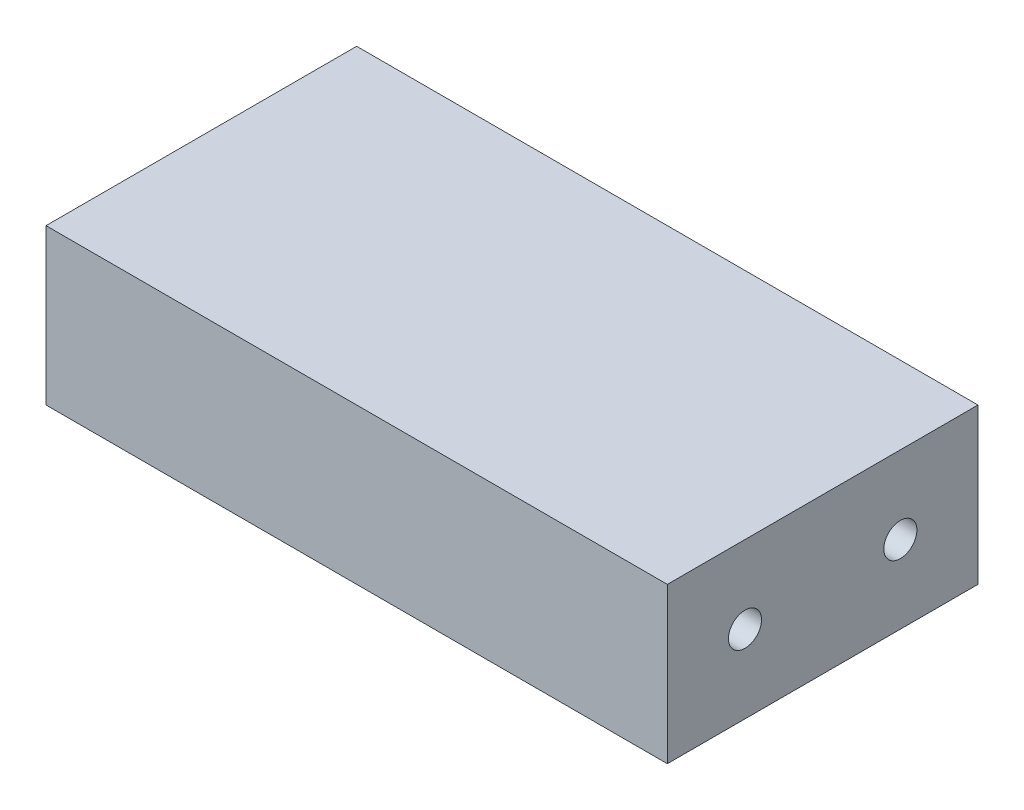
SolidWorks part; units mm, degrees
ref_plane "Front Plane" through (0, 0, 0) normal (0, 0, 1) x (1, 0, 0)
ref_plane "Top Plane" through (0, 0, 0) normal (0, 1, 0) x (1, 0, 0)
ref_plane "Right Plane" through (0, 0, 0) normal (1, 0, 0) x (0, 0, -1)
sketch "Sketch1" plane through (0, 0, 0) normal (0, 1, 0) x (1, 0, 0)
  line L0 (-26, 19.0667) -> (-26, -6.3333)
  line L1 (-26, -6.3333) -> (24.8, -6.3333)
  line L2 (24.8, -6.3333) -> (24.8, 19.0667)
  line L3 (24.8, 19.0667) -> (-26, 19.0667)
  dimension "D1" = 50.8
  dimension "D2" = 25.4
extrude "Boss-Extrude1" add sketch "Sketch1" along normal blind 12.7
hole_wizard "#6-32 Tapped Hole1" positions "Sketch7" profile "Sketch3" tap size "#6-32" standard "ANSI Inch"
sketch "Sketch7" plane through (24.8, 0, 0) normal (1, 0, 0) x (0, 0, -1)
  line L0 (-6.3333, 12.7) -> (-6.3333, 0) construction
  line L1 (-6.3333, 12.7) -> (19.0667, 12.7) construction
  line L2 (19.0667, 12.7) -> (19.0667, 0) construction
  point P0 (0.0167, 6.35)
  point P2 (12.7167, 6.35)
  point P13 (14.7257, 6.35)
  dimension "D1" = 6.35
  dimension "D2" = 6.35
  dimension "D3" = 6.35
  dimension "D4" = 6.35
sketch "Sketch3" plane through (24.8, 6.35, -0.0167) normal (0, 1, 0) x (0, 0, -1)
  line L0 (0, 0) -> (0, 13.5127)
  line L1 (0, 13.5127) -> (1.3525, 12.7)
  line L2 (1.3525, 12.7) -> (1.3525, 0)
  line L5 (1.3525, 0) -> (0, 0)
  line L10 (0, 13.5127) -> (-1.3526, 12.7) construction
  line L11 (0, -6.35) -> (0, 107.95) construction
  dimension "Tap Drill Dia." = 2.7051
  dimension "Tap Drill Depth" = 12.7
  dimension "Drill Angle" = 118
ref_plane "Plane1" through (-0.6, 0, 0) normal (1, 0, 0) x (0, 0, -1)
mirror "Mirror1" about plane through (-0.6, 0, 0) normal (1, 0, 0) of "#6-32 Tapped Hole1"
